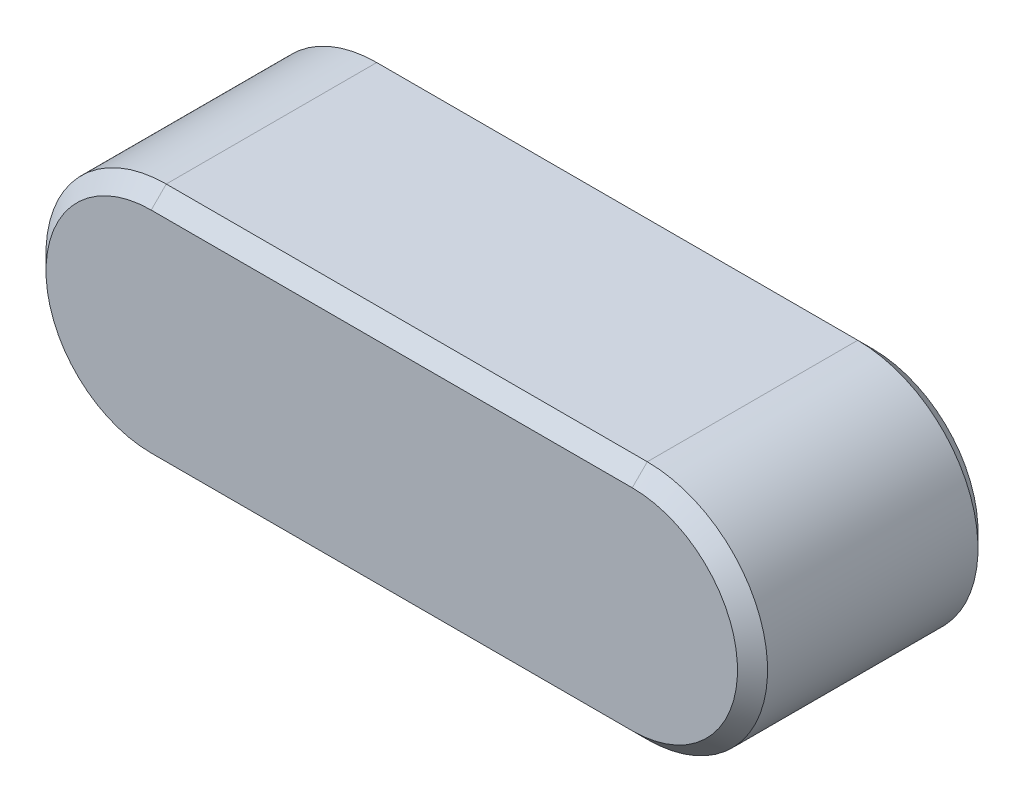
SolidWorks part; units mm, degrees
ref_plane "Front" through (0, 0, 0) normal (0, 0, 1) x (1, 0, 0)
ref_plane "Top" through (0, 0, 0) normal (0, 1, 0) x (1, 0, 0)
ref_plane "Right" through (0, 0, 0) normal (1, 0, 0) x (0, 0, -1)
sketch "Sketch1" plane through (0, 0, 0) normal (0, 0, 1) x (1, 0, 0)
  line L0 (-8, 2) -> (0, 2)
  line L1 (0, -2) -> (-8, -2)
  arc A0 (0, 2) -> (0, -2) centre (0, 0) cw
  arc A1 (-8, -2) -> (-8, 2) centre (-8, 0) cw
  dimension "L" = 12
  dimension "b" = 4
extrude "BaseKey" add sketch "Sketch1" along normal mid plane 4
sketch "Sketch2" plane through (0, 0, 0) normal (0, 0, 1) x (1, 0, 0)
  line L1 (-10, 2) -> (2, 2)
  line L2 (-10, 2) -> (-10, -2)
  line L3 (-10, -2) -> (2, -2)
  line L4 (2, 2) -> (2, -2)
  line L6 (0, -2) -> (-8, -2) construction
  line L7 (-8, 2) -> (0, 2) construction
  arc A2 (0, -2) -> (0, 2) centre (0, 0) ccw construction
  arc A3 (-8, 2) -> (-8, -2) centre (-8, 0) ccw construction
extrude "Extrude1" [suppressed] add sketch "Sketch2" along normal mid plane 4
sketch "Sketch3" plane through (0, 0, 0) normal (0, 0, 1) x (1, 0, 0)
  line L0 (2, 2) -> (-8, 2)
  line L1 (-8, -2) -> (2, -2)
  line L2 (2, -2) -> (2, 2)
  line L5 (-8, 2) -> (0, 2) construction
  arc A0 (-8, 2) -> (-8, -2) centre (-8, 0) ccw
  arc A1 (0, -2) -> (0, 2) centre (0, 0) ccw construction
  arc A4 (-8, 2) -> (-8, -2) centre (-8, 0) ccw construction
extrude "Extrude2" [suppressed] add sketch "Sketch3" along normal mid plane 4
chamfer "Chamfer1" distance 0.25 angle 45 8 edges at (2, 0, -2) (-4, -2, -2) (-10, 0, -2) (-4, 2, -2) (-10, 0, 2) (-4, -2, 2) (2, 0, 2) (-4, 2, 2)
equation "\"D1@Extrude1\"=\"h@BaseKey\""
equation "\"D1@Extrude2\"=\"h@BaseKey\""
